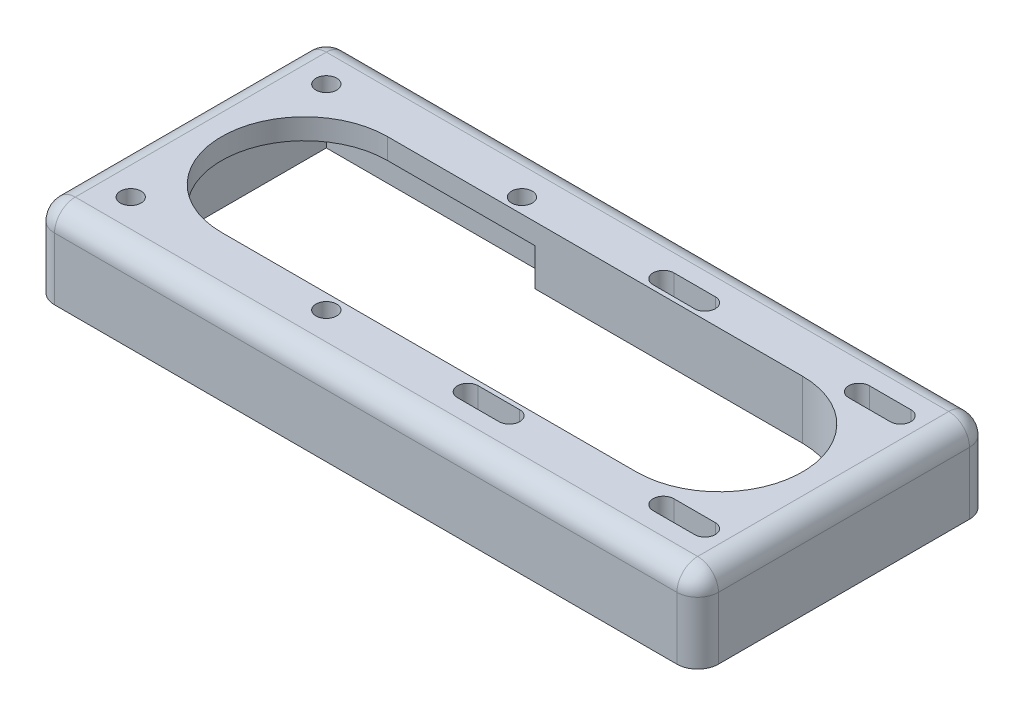
SolidWorks part; units mm, degrees
ref_plane "Front Plane" through (0, 0, 0) normal (0, 0, 1) x (1, 0, 0)
ref_plane "Top Plane" through (0, 0, 0) normal (0, 1, 0) x (1, 0, 0)
ref_plane "Right Plane" through (0, 0, 0) normal (1, 0, 0) x (0, 0, -1)
sketch "Sketch2" plane through (0, 0, 0) normal (0, 1, 0) x (1, 0, 0)
  line L0 (-75, 0) -> (-14.5, 0) construction
  line L1 (-75, 30.25) -> (75, 30.25)
  line L2 (-75, 30.25) -> (-75, -30.25)
  line L3 (-75, -30.25) -> (75, -30.25)
  line L4 (75, 30.25) -> (75, -30.25)
  line L5 (-75, 30.25) -> (75, -30.25) construction
  line L6 (-75, -30.25) -> (75, 30.25) construction
  line L11 (75, 30.25) -> (8, 30.25)
  line L12 (75, 30.25) -> (75, 28.5)
  line L13 (75, 28.5) -> (8, 28.5)
  line L14 (8, 30.25) -> (8, 28.5)
  line L15 (8, -30.25) -> (8, -28.5)
  line L16 (75, -28.5) -> (8, -28.5)
  line L17 (75, -30.25) -> (75, -28.5)
  line L18 (75, -30.25) -> (8, -30.25)
  line L19 (-44.75, 0) -> (-44.75, 30.25) construction
  line L20 (41.5, 28.5) -> (41.5, -28.5) construction
  line L22 (41.5, 0) -> (75, 0) construction
  line L23 (60.07, 26.07) -> (70.07, 26.07)
  line L24 (60.07, 26.07) -> (60.07, 21.07)
  line L25 (60.07, 21.07) -> (70.07, 21.07)
  line L26 (70.07, 26.07) -> (70.07, 21.07)
  line L27 (60.07, 26.07) -> (70.07, 21.07) construction
  line L28 (60.07, 21.07) -> (70.07, 26.07) construction
  line L29 (-75, 30.25) -> (-14.5, 30.25)
  line L34 (-75, 30.25) -> (-75, -30.25)
  line L35 (-75, -30.25) -> (-14.5, -30.25)
  line L36 (-14.5, 30.25) -> (-14.5, -30.25)
  line L37 (-50, 20) -> (50, 20)
  line L53 (-50, 20) -> (-50, -20)
  line L54 (-50, -20) -> (50, -20)
  line L55 (50, 20) -> (50, -20)
  line L56 (-50, 20) -> (50, -20) construction
  line L57 (-50, -20) -> (50, 20) construction
  line L58 (22.93, 26.07) -> (12.93, 21.07) construction
  line L59 (22.93, 21.07) -> (12.93, 26.07) construction
  line L60 (22.93, 21.07) -> (12.93, 21.07)
  line L61 (12.93, 26.07) -> (12.93, 21.07)
  line L62 (22.93, 26.07) -> (12.93, 26.07)
  line L63 (22.93, 26.07) -> (22.93, 21.07)
  line L64 (22.93, -21.07) -> (12.93, -26.07) construction
  line L65 (22.93, -26.07) -> (12.93, -21.07) construction
  line L66 (60.07, -21.07) -> (70.07, -26.07) construction
  line L67 (60.07, -26.07) -> (70.07, -21.07) construction
  line L68 (22.93, -26.07) -> (22.93, -21.07)
  line L69 (22.93, -26.07) -> (12.93, -26.07)
  line L70 (12.93, -26.07) -> (12.93, -21.07)
  line L71 (22.93, -21.07) -> (12.93, -21.07)
  line L72 (70.07, -26.07) -> (70.07, -21.07)
  line L73 (60.07, -21.07) -> (70.07, -21.07)
  line L74 (60.07, -26.07) -> (60.07, -21.07)
  line L75 (60.07, -26.07) -> (70.07, -26.07)
  circle A14 centre (-68.32, 23.57) radius 2.5
  circle A23 centre (60.07, 23.57) radius 2.5
  circle A24 centre (70.07, 23.57) radius 2.5
  circle A33 centre (-50, 0) radius 20
  circle A34 centre (50, 0) radius 20
  circle A35 centre (-21.18, 23.57) radius 2.5
  circle A36 centre (-21.18, -23.57) radius 2.5
  circle A37 centre (-68.32, -23.57) radius 2.5
  circle A38 centre (12.93, 23.57) radius 2.5
  circle A39 centre (22.93, 23.57) radius 2.5
  circle A40 centre (22.93, -23.57) radius 2.5
  circle A41 centre (12.93, -23.57) radius 2.5
  circle A42 centre (70.07, -23.57) radius 2.5
  circle A43 centre (60.07, -23.57) radius 2.5
  point P16 (65.07, 23.57)
  point P25 (0, 0)
  point P38 (75, 0)
  point P74 (65.07, -23.57)
  dimension "D5" = 6.68
  dimension "D8" = 4.93
  dimension "D11" = 40
  dimension "D7" = 5
  dimension "D1" = 60.5
  dimension "D2" = 150
  dimension "D3" = 67
  dimension "D4" = 100
  dimension "D6" = 6.68
  dimension "D9" = 5
  dimension "D10" = 10
  dimension "D13" = 4.93
extrude "Boss-Extrude1" add sketch "Sketch2" along normal blind 5 contours A33 L37 L36 L1 L2 L3 L54 A35 A14 A36 A37 | A34 L54 L36 L3 L15 L16 L4 L13 L14 L1 L37 A41 L71 A40 L69 A24 L25 A23 L23 L62 A39 L60 A38 L75 A43 L73 A42 | L4 L16 L15 L3 | L1 L14 L13 L4
sketch "Sketch4" plane through (0, 5, 0) normal (0, 1, 0) x (1, 0, 0)
  line L49 (-80, 35.25) -> (80, 35.25)
  line L50 (-75, 30.25) -> (75, 30.25)
  line L51 (-75, 30.25) -> (-75, -30.25)
  line L52 (-75, -30.25) -> (75, -30.25)
  line L53 (75, 30.25) -> (75, -30.25)
  line L54 (80, 35.25) -> (80, -35.25)
  line L55 (-80, -35.25) -> (80, -35.25)
  line L56 (-80, 35.25) -> (-80, -35.25)
  dimension "D1" = 5
extrude "Boss-Extrude2" add sketch "Sketch4" against normal blind 20
sketch "Sketch5" plane through (0, 0, 0) normal (0, -1, 0) x (-1, 0, 0)
  line L5 (75, -30.25) -> (-75, -30.25) construction
  line L31 (-8, 30.25) -> (14.5, 30.25)
  line L34 (-8, 30.25) -> (-8, -30.25)
  line L45 (75, -30.25) -> (-75, -30.25) construction
  line L54 (-8, -30.25) -> (14.5, -30.25)
  line L55 (-50, -20) -> (-50, 20) construction
  line L56 (-17.93, -26.07) -> (-17.93, -21.07) construction
  line L57 (34, 20) -> (-50, 20)
  line L58 (-75, 30.25) -> (-8, 30.25)
  line L59 (-75, 30.25) -> (-75, -30.25)
  line L60 (-75, -30.25) -> (-8, -30.25)
  line L61 (-8, 30.25) -> (-8, -30.25)
  line L62 (34, 20) -> (34, -20)
  line L63 (34, -20) -> (-50, -20)
  line L64 (-50, 20) -> (-50, -20)
  line L65 (34, 20) -> (-50, -20) construction
  line L66 (34, -20) -> (-50, 20) construction
  line L67 (-22.93, -26.07) -> (-12.93, -26.07) construction
  line L68 (-22.93, -21.07) -> (-12.93, -21.07) construction
  line L69 (-8, 0) -> (-75, 0) construction
  line L70 (-41.5, -30.25) -> (-41.5, 30.25) construction
  line L71 (-70.07, -21.07) -> (-60.07, -26.07) construction
  line L72 (-12.93, -26.07) -> (-22.93, -26.07)
  line L73 (-12.93, -26.07) -> (-12.93, -21.07)
  line L74 (-12.93, -21.07) -> (-22.93, -21.07)
  line L75 (-22.93, -26.07) -> (-22.93, -21.07)
  line L76 (-12.93, -26.07) -> (-22.93, -21.07) construction
  line L77 (-12.93, -21.07) -> (-22.93, -26.07) construction
  line L78 (-70.07, -26.07) -> (-60.07, -21.07) construction
  line L79 (-65.07, -26.07) -> (-65.07, -21.07) construction
  line L80 (-60.07, -26.07) -> (-60.07, -21.07)
  line L81 (-70.07, -21.07) -> (-60.07, -21.07)
  line L82 (-70.07, -26.07) -> (-70.07, -21.07)
  line L83 (-70.07, -26.07) -> (-60.07, -26.07)
  line L84 (-65.07, 26.07) -> (-65.07, 21.07) construction
  line L85 (-70.07, 26.07) -> (-60.07, 21.07) construction
  line L86 (-12.93, 21.07) -> (-22.93, 26.07) construction
  line L87 (-12.93, 26.07) -> (-22.93, 21.07) construction
  line L88 (-70.07, 21.07) -> (-60.07, 26.07) construction
  line L89 (-17.93, 26.07) -> (-17.93, 21.07) construction
  line L90 (-70.07, 26.07) -> (-60.07, 26.07)
  line L91 (-70.07, 26.07) -> (-70.07, 21.07)
  line L92 (-70.07, 21.07) -> (-60.07, 21.07)
  line L93 (-60.07, 26.07) -> (-60.07, 21.07)
  line L94 (-22.93, 26.07) -> (-22.93, 21.07)
  line L95 (-12.93, 21.07) -> (-22.93, 21.07)
  line L96 (-12.93, 26.07) -> (-12.93, 21.07)
  line L97 (-12.93, 26.07) -> (-22.93, 26.07)
  line L98 (14.5, 30.25) -> (14.5, -30.25)
  line L99 (75, 30.25) -> (75, -30.25) construction
  circle A23 centre (-50, 0) radius 20
  circle A24 centre (-22.93, -23.57) radius 2.5
  circle A25 centre (-12.93, -23.57) radius 2.5
  circle A26 centre (-70.07, -23.57) radius 2.5
  circle A27 centre (-60.07, -23.57) radius 2.5
  circle A28 centre (-60.07, 23.57) radius 2.5
  circle A29 centre (-70.07, 23.57) radius 2.5
  circle A30 centre (-12.93, 23.57) radius 2.5
  circle A31 centre (-22.93, 23.57) radius 2.5
  point P10 (-8, 0)
  point P23 (-17.93, -23.57)
  point P42 (-65.07, -23.57)
  point P60 (14.5, 0)
  point P68 (-65.07, 23.57)
  point P69 (-17.93, 23.57)
  arc M5 (-70.07, 21.07) -> (-70.07, 26.07) centre (-70.07, 23.57) cw
  arc M10 (-50, -20) -> (-50, 20) centre (-50, 0) cw
  line M14 (-75, -30.25) -> (75, -30.25)
  line M16 (75, 30.25) -> (-75, 30.25)
  line M19 (-75, 30.25) -> (-75, -30.25)
  arc M22 (-60.07, 26.07) -> (-60.07, 21.07) centre (-60.07, 23.57) cw
  line M32 (-70.07, 26.07) -> (-60.07, 26.07)
  line M33 (-60.07, 21.07) -> (-70.07, 21.07)
  arc M127 (-12.93, -21.07) -> (-12.93, -26.07) centre (-12.93, -23.57) cw
  line M128 (-12.93, -26.07) -> (-22.93, -26.07)
  arc M129 (-22.93, -26.07) -> (-22.93, -21.07) centre (-22.93, -23.57) cw
  line M130 (-22.93, -21.07) -> (-12.93, -21.07)
  line M131 (-50, 20) -> (50, 20)
  line M134 (50, -20) -> (-50, -20)
  line M135 (-22.93, 26.07) -> (-12.93, 26.07)
  arc M136 (-12.93, 26.07) -> (-12.93, 21.07) centre (-12.93, 23.57) cw
  line M137 (-12.93, 21.07) -> (-22.93, 21.07)
  arc M138 (-22.93, 21.07) -> (-22.93, 26.07) centre (-22.93, 23.57) cw
  line M139 (-60.07, -26.07) -> (-70.07, -26.07)
  arc M140 (-70.07, -26.07) -> (-70.07, -21.07) centre (-70.07, -23.57) cw
  line M141 (-70.07, -21.07) -> (-60.07, -21.07)
  arc M142 (-60.07, -21.07) -> (-60.07, -26.07) centre (-60.07, -23.57) cw
  dimension "D1" = 67
  dimension "D2" = 60.5
extrude "Boss-Extrude3" add sketch "Sketch5" along normal blind 9 contours L61 M16 M19 M14 M134 M10 M131 M130 M127 M128 M129 M33 M5 M32 M22 M138 M135 M136 M137 M142 M139 M140 M141 | L98 L34 M16 M131 | L98 L63 L34 M14
fillet "Fillet2" radius 5 8 edges at (-80, -5, -35.25) (80, -5, 35.25) (80, -5, -35.25) (80, 5, 0) (0, 5, -35.25) (-80, 5, 0) (-80, -5, 35.25) (0, 5, 35.25)
